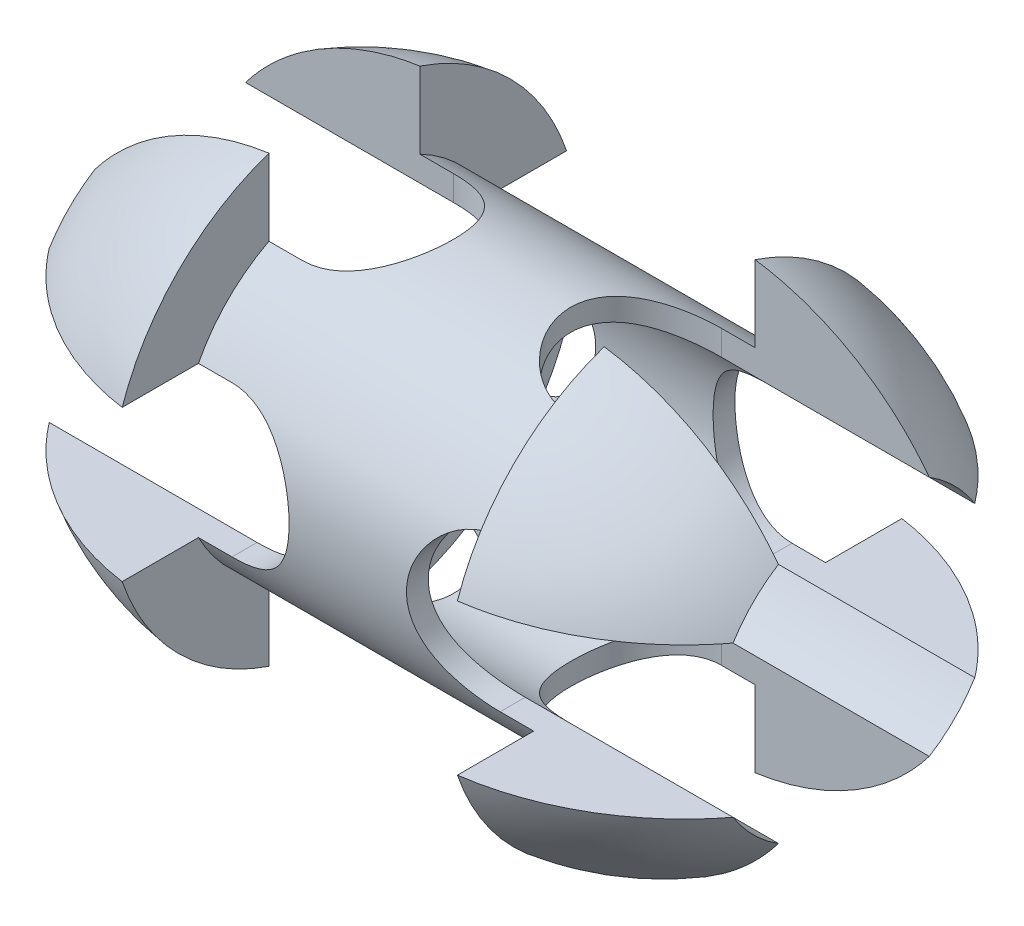
SolidWorks part; units mm, degrees
ref_plane "Front Plane" through (0, 0, 0) normal (0, 0, 1) x (1, 0, 0)
ref_plane "Top Plane" through (0, 0, 0) normal (0, 1, 0) x (1, 0, 0)
ref_plane "Right Plane" through (0, 0, 0) normal (1, 0, 0) x (0, 0, -1)
sketch "Sketch1" plane through (0, 0, 0) normal (0, 0, 1) x (1, 0, 0)
  line L0 (0, -29.1631) -> (0, 41.977) construction
  line L1 (-10, 9.8) -> (10, 9.8)
  line L2 (10, 9.8) -> (10, 14)
  line L3 (24.5, 0) -> (7, 0)
  line L4 (-3.1225, 0) -> (36.3968, 0) construction
  line L5 (7, 0) -> (-7, 0)
  line L6 (0, 0) -> (7, 0)
  line L7 (-24.5, 0) -> (-7, 0)
  line L8 (-10, 9.8) -> (-10, 14)
  arc A0 (10, 14) -> (24.5, 0) centre (7.7405, -2.8492) cw
  arc A1 (-10, 14) -> (-24.5, 0) centre (-7.7405, -2.8492) ccw
  point P17 (0, 9.8)
  dimension "D7" = 17
  dimension "D8" = 9.8
  dimension "D2" = 24.5
  dimension "D3" = 10
  dimension "D4" = 0
  dimension "D5" = 14
  dimension "D6" = 7
revolve "Revolve4" add sketch "Sketch1" angle 360 about L4
sketch "Sketch2" plane through (0, 0, 0) normal (0, 0, 1) x (1, 0, 0)
  line L0 (29, 4.5) -> (29, -4.5)
  line L1 (29, -4.5) -> (8, -4.5)
  line L2 (29, 4.5) -> (8, 4.5)
  line L3 (0, 0) -> (0, 15.0761) construction
  line L4 (-29, 4.5) -> (-29, -4.5)
  line L5 (-29, 4.5) -> (-8, 4.5)
  line L6 (-29, -4.5) -> (-8, -4.5)
  arc A0 (8, 4.5) -> (8, -4.5) centre (8, 0) ccw
  arc A1 (-8, 4.5) -> (-8, -4.5) centre (-8, 0) cw
  dimension "D3" = 29
  dimension "D1" = 9
  dimension "D2" = 4.5
  dimension "D4" = 8
  dimension "D5" = 0
extrude "Cut-Extrude1" cut sketch "Sketch2" against normal mid plane 30
sketch "Sketch3" plane through (0, 0, 0) normal (0, 1, 0) x (1, 0, 0)
  line L0 (0, 0) -> (0, 8.4685) construction
  line L1 (29, 4.5) -> (29, -4.5)
  line L2 (29, -4.5) -> (8, -4.5)
  line L3 (29, 4.5) -> (8, 4.5)
  line L4 (-29, -4.5) -> (-8, -4.5)
  line L5 (-29, 4.5) -> (-29, -4.5)
  line L6 (-29, 4.5) -> (-8, 4.5)
  arc A0 (8, -4.5) -> (8, 4.5) centre (8, 0) cw
  arc A1 (-8, -4.5) -> (-8, 4.5) centre (-8, 0) ccw
  dimension "D1" = 9
  dimension "D2" = 8
  dimension "D3" = 0
  dimension "D4" = 29
  dimension "D5" = 4.5
extrude "Cut-Extrude2" cut sketch "Sketch3" against normal mid plane 30
sketch "Sketch4" plane through (0, 0, 0) normal (1, 0, 0) x (0, 0, -1)
  circle A0 centre (0, 0) radius 8.5
  dimension "D1" = 17
extrude "Cut-Extrude3" cut sketch "Sketch4" against normal mid plane 60
